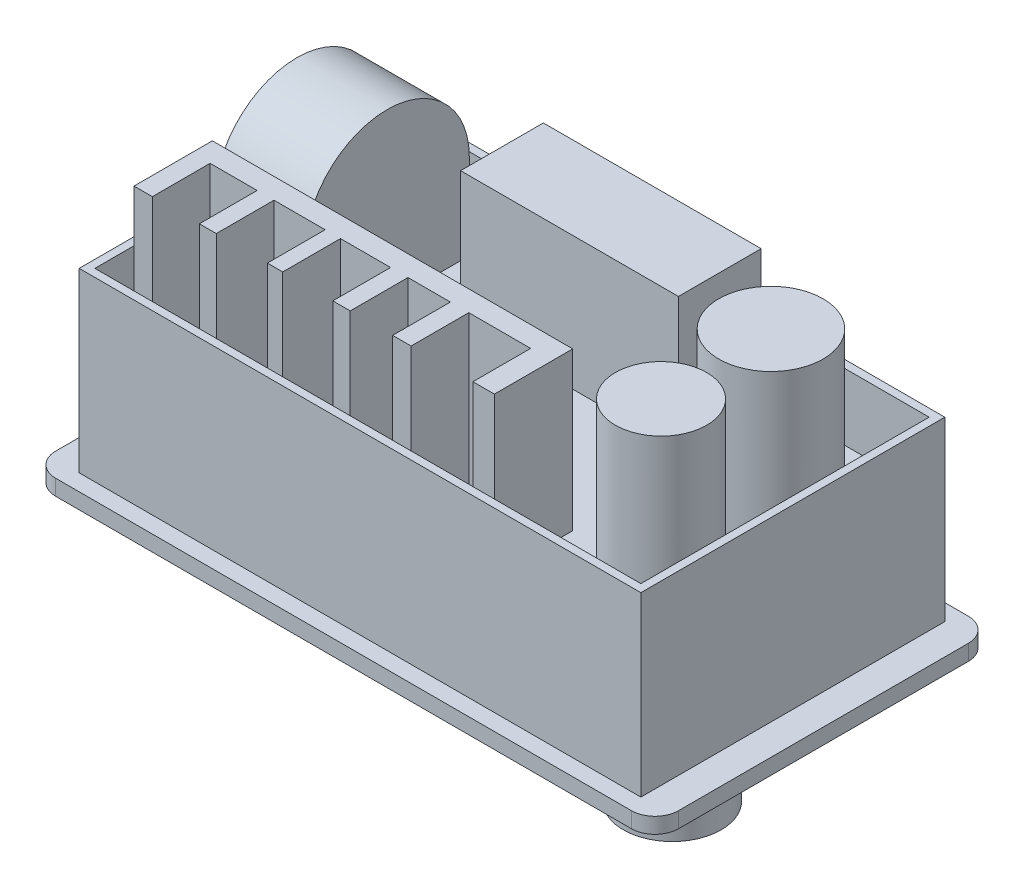
SolidWorks part; units mm, degrees
ref_plane "Front Plane" through (0, 0, 0) normal (0, 0, 1) x (1, 0, 0)
ref_plane "Top Plane" through (0, 0, 0) normal (0, 1, 0) x (1, 0, 0)
ref_plane "Right Plane" through (0, 0, 0) normal (1, 0, 0) x (0, 0, -1)
sketch "Sketch1" plane through (0, 0, 0) normal (0, 1, 0) x (1, 0, 0)
  line L1 (-14.6751, 3.6977) -> (64.8249, 3.6977)
  line L2 (-14.6751, 3.6977) -> (-14.6751, -39.3023)
  line L3 (-14.6751, -39.3023) -> (64.8249, -39.3023)
  line L4 (64.8249, 3.6977) -> (64.8249, -39.3023)
  dimension "D1" = 43
  dimension "D2" = 79.5
extrude "Boss-Extrude1" add sketch "Sketch1" along normal blind 2
sketch "Sketch2" plane through (0, 2, 0) normal (0, 1, 0) x (1, 0, 0)
  line L0 (64.8249, -39.3023) -> (64.8249, 3.6977) construction
  line L1 (-10.7751, 1.5977) -> (60.9249, 1.5977)
  line L2 (-10.7751, 1.5977) -> (-10.7751, -37.2023)
  line L3 (-10.7751, -37.2023) -> (60.9249, -37.2023)
  line L4 (60.9249, 1.5977) -> (60.9249, -37.2023)
  line L5 (-14.6751, 3.6977) -> (-14.6751, -39.3023) construction
  line L6 (-14.6751, -39.3023) -> (64.8249, -39.3023) construction
  line L7 (64.8249, 3.6977) -> (-14.6751, 3.6977) construction
  dimension "D1" = 3.9
  dimension "D2" = 3.9
  dimension "D3" = 2.1
  dimension "D4" = 2.1
extrude "Boss-Extrude2" add sketch "Sketch2" along normal blind 22.6
sketch "Sketch3" plane through (0, 24.6, 0) normal (0, 1, 0) x (1, 0, 0)
  line L0 (60.9249, -37.2023) -> (60.9249, 1.5977) construction
  line L1 (-9.7751, 0.5977) -> (59.9249, 0.5977)
  line L2 (-9.7751, 0.5977) -> (-9.7751, -36.2023)
  line L3 (-9.7751, -36.2023) -> (59.9249, -36.2023)
  line L4 (59.9249, 0.5977) -> (59.9249, -36.2023)
  line L5 (-10.7751, -37.2023) -> (60.9249, -37.2023) construction
  line L6 (-10.7751, 1.5977) -> (-10.7751, -37.2023) construction
  line L7 (60.9249, 1.5977) -> (-10.7751, 1.5977) construction
  dimension "D1" = 1
  dimension "D2" = 1
  dimension "D3" = 1
  dimension "D4" = 1
extrude "Cut-Extrude1" cut sketch "Sketch3" against normal blind 8.5
sketch "Sketch5" plane through (0, 16.1, 0) normal (0, 1, 0) x (1, 0, 0)
  line L0 (-9.7751, -36.2023) -> (59.9249, -36.2023) construction
  line L1 (-4.7751, -26.2023) -> (41.2249, -26.2023)
  line L2 (-4.7751, -26.2023) -> (-4.7751, -36.2023)
  line L3 (-4.7751, -36.2023) -> (41.2249, -36.2023)
  line L4 (41.2249, -26.2023) -> (41.2249, -36.2023)
  line L5 (-9.7751, 0.5977) -> (-9.7751, -36.2023) construction
  line L7 (-2.433, -28.8316) -> (3.5711, -28.8316)
  line L8 (-2.433, -28.8316) -> (-2.433, -36.2023)
  line L9 (-2.433, -36.2023) -> (3.5711, -36.2023)
  line L10 (3.5711, -28.8316) -> (3.5711, -36.2023)
  line L11 (5.7247, -28.8316) -> (12.2509, -28.8316)
  line L12 (5.7247, -28.8316) -> (5.7247, -36.2023)
  line L13 (5.7247, -36.2023) -> (12.2509, -36.2023)
  line L14 (12.2509, -28.8316) -> (12.2509, -36.2023)
  line L15 (14.2088, -28.8316) -> (20.6044, -28.8316)
  line L16 (14.2088, -28.8316) -> (14.2088, -36.2023)
  line L17 (14.2088, -36.2023) -> (20.6044, -36.2023)
  line L18 (20.6044, -28.8316) -> (20.6044, -36.2023)
  line L19 (22.8233, -28.8316) -> (28.2401, -28.8316)
  line L20 (22.8233, -28.8316) -> (22.8233, -36.2023)
  line L21 (22.8233, -36.2023) -> (28.2401, -36.2023)
  line L22 (28.2401, -28.8316) -> (28.2401, -36.2023)
  line L23 (30.5895, -28.8316) -> (38.4862, -28.8316)
  line L24 (30.5895, -28.8316) -> (30.5895, -36.2023)
  line L25 (30.5895, -36.2023) -> (38.4862, -36.2023)
  line L26 (38.4862, -28.8316) -> (38.4862, -36.2023)
  line M10 (-9.7751, -36.2023) -> (59.9249, -36.2023)
  dimension "D1" = 46
  dimension "D2" = 10
  dimension "D3" = 5
extrude "Boss-Extrude3" add sketch "Sketch5" along normal blind 22.6 contours L23 L26 L4 L1 L2 L8 L7 L10 L12 L11 L14 L16 L15 L18 L20 L19 L22 L24 M10
sketch "Sketch6" plane through (0, 0, 37.2023) normal (0, 0, 1) x (1, 0, 0)
  line L0 (-10.7751, 24.6) -> (60.9249, 24.6) construction
  line L1 (-14.637, 45.1409) -> (52.5827, 45.1409)
  line L2 (-14.637, 45.1409) -> (-14.637, 36.2)
  line L3 (-14.637, 36.2) -> (52.5827, 36.2)
  line L4 (52.5827, 45.1409) -> (52.5827, 36.2)
  dimension "D1" = 11.6
extrude "Cut-Extrude2" cut sketch "Sketch6" against normal blind 22.6
sketch "Sketch7" plane through (0, 16.1, 0) normal (0, 1, 0) x (1, 0, 0)
  circle A0 centre (51.669, -11.3414) radius 6.6637
  circle A1 centre (52.3869, -26.0906) radius 5.8292
extrude "Boss-Extrude4" add sketch "Sketch7" along normal up to surface (20.1 mm away) up to face at (17.543, 36.2, 32.2978)
fillet "Fillet1" radius 3 4 edges at (-14.6751, 1, -3.6977) (64.8249, 1, -3.6977) (64.8249, 1, 39.3023) (-14.6751, 1, 39.3023)
sketch "Sketch8" plane through (0, 16.1, 0) normal (0, 1, 0) x (1, 0, 0)
  line L1 (11.272, 0) -> (39.0735, 0)
  line L2 (11.272, 0) -> (11.272, -10.5583)
  line L3 (11.272, -10.5583) -> (39.0735, -10.5583)
  line L4 (39.0735, 0) -> (39.0735, -10.5583)
extrude "Boss-Extrude5" add sketch "Sketch8" along normal blind 17
sketch "Sketch9" plane through (0, 0, 0) normal (0, -1, 0) x (1, 0, 0)
  line L0 (64.8249, 36.3023) -> (64.8249, -0.6977) construction
  line L1 (-8.6751, 33.3023) -> (58.8249, 33.3023)
  line L2 (-8.6751, 33.3023) -> (-8.6751, 2.3023)
  line L3 (-8.6751, 2.3023) -> (58.8249, 2.3023)
  line L4 (58.8249, 33.3023) -> (58.8249, 2.3023)
  line L5 (61.8249, -3.6977) -> (-11.6751, -3.6977) construction
  line L6 (-14.6751, -0.6977) -> (-14.6751, 36.3023) construction
  line L7 (-11.6751, 39.3023) -> (61.8249, 39.3023) construction
  dimension "D1" = 6
  dimension "D2" = 6
  dimension "D3" = 6
  dimension "D4" = 6
extrude "Cut-Extrude3" cut sketch "Sketch9" against normal blind 1
sketch "Sketch10" plane through (0, 1, 0) normal (0, -1, 0) x (1, 0, 0)
  line L1 (4.1584, 30.5936) -> (33.0042, 30.5936)
  line L2 (4.1584, 30.5936) -> (4.1584, 4.6194)
  line L3 (4.1584, 4.6194) -> (33.0042, 4.6194)
  line L4 (33.0042, 30.5936) -> (33.0042, 4.6194)
extrude "Cut-Extrude4" cut sketch "Sketch10" against normal blind 1
sketch "Sketch11" plane through (0, 1, 0) normal (0, -1, 0) x (1, 0, 0)
  circle A0 centre (50.4291, 22.697) radius 6.25
  dimension "D1" = 12.5
extrude "Boss-Extrude6" add sketch "Sketch11" along normal blind 12 contours A0
sketch "Sketch12" plane through (-9.7751, 0, 0) normal (1, 0, 0) x (0, 0, -1)
  line L0 (-12.9023, 16.1) -> (-12.9023, 27) construction
  line L1 (0.5977, 16.1) -> (-36.2023, 16.1) construction
  line L2 (-23.4023, 16.1) -> (-23.4023, 27)
  line L3 (-2.4023, 16.1) -> (-2.4023, 27)
  line L4 (-36.3023, 0) -> (0.6977, 0) construction
  arc A0 (-23.4023, 16.1) -> (-2.4023, 16.1) centre (-12.9023, 16.1) ccw
  arc A1 (-2.4023, 27) -> (-23.4023, 27) centre (-12.9023, 27) ccw
  point P4 (-12.9023, 21.55)
  point P9 (-12.9023, 37.5)
  dimension "D1" = 10.5
  dimension "D2" = 4
  dimension "D3" = 37.5
extrude "Boss-Extrude7" add sketch "Sketch12" along normal offset from surface (11.5 mm away) 15 from offset 2.5 up to face at (-10.7751, 13.3, 17.8023)
